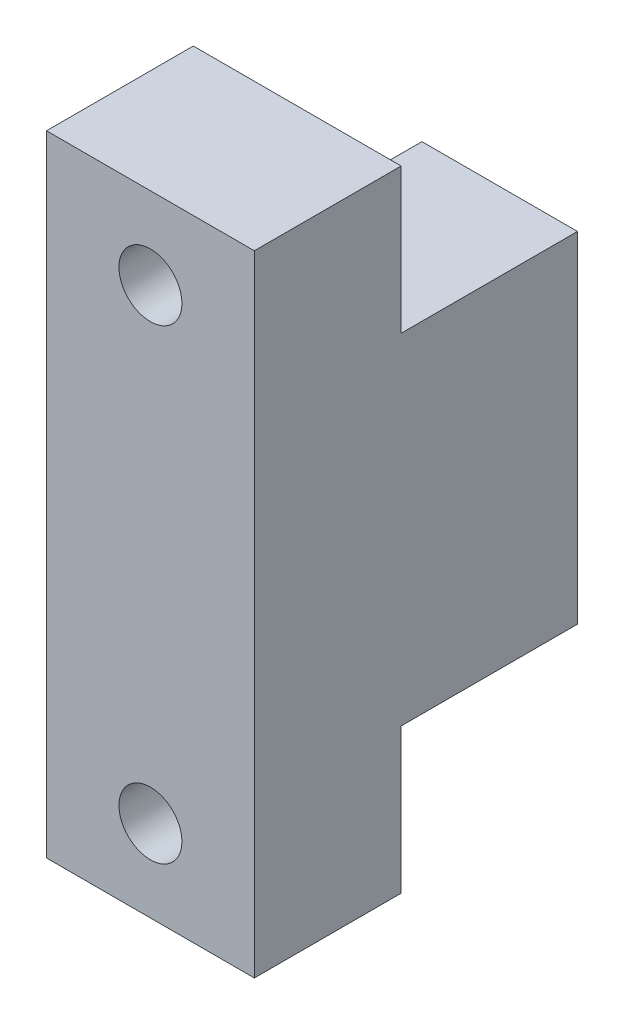
SolidWorks part; units mm, degrees
ref_plane "Front Plane" through (0, 0, 0) normal (0, 0, 1) x (1, 0, 0)
ref_plane "Top Plane" through (0, 0, 0) normal (0, 1, 0) x (1, 0, 0)
ref_plane "Right Plane" through (0, 0, 0) normal (1, 0, 0) x (0, 0, -1)
sketch "Sketch2" plane through (0, 0, 0) normal (0, 0, 1) x (1, 0, 0)
  line L0 (5.5262, -15.0933) -> (5.5262, 34.9067)
  line L1 (-10.9738, -15.0933) -> (5.5262, -15.0933)
  line L2 (-10.9738, 34.9067) -> (5.5262, 34.9067)
  line L23 (-10.9738, 34.9067) -> (-10.9738, -15.0933)
  circle A2 centre (-2.7238, -8.5933) radius 2.5
  circle A3 centre (-2.7238, 28.4067) radius 2.5
  dimension "D1" = 5
  dimension "D3" = 5
  dimension "D2" = 6.5
  dimension "D4" = 50
  dimension "D5" = 6.5
extrude "Boss-Extrude1" add sketch "Sketch2" along normal blind 11.655
sketch "Sketch4" plane through (0, 0, 11.655) normal (0, 0, 1) x (1, 0, 0)
  circle A31 centre (-2.7238, 28.4067) radius 4.5
  circle A32 centre (-2.7238, 28.4067) radius 4.5
  circle A34 centre (-2.7238, -8.5933) radius 4.5
  circle A35 centre (-2.7238, -8.5933) radius 4.5
  dimension "D1" = 2
  dimension "D2" = 2
extrude "Cut-Extrude3" cut sketch "Sketch4" against normal blind 10 from offset 7 offset against normal yes
sketch "Sketch6" plane through (0, 0, 0) normal (0, 0, -1) x (-1, 0, 0)
  line L0 (10.9738, 34.9067) -> (10.9738, -15.0933) construction
  line L1 (6.8238, 23.4067) -> (-5.5262, 23.4067)
  line L3 (6.8238, -3.5933) -> (6.8238, 23.4067)
  line L4 (6.8238, -3.5933) -> (-5.5262, -3.5933)
  line L6 (-5.5262, 23.4067) -> (-5.5262, -3.5933)
  point P4 (0, 0)
  point P12 (6.8238, -3.9751)
  dimension "D2" = 4.15
  dimension "D4" = 16.5
  dimension "D5" = 11.5
  dimension "D8" = 38.5
extrude "Boss-Extrude2" add sketch "Sketch6" along normal up to surface (6 mm away)
sketch "Sketch7" plane through (0, 0, -6) normal (0, 0, -1) x (-1, 0, 0)
  circle A2 centre (2.7238, 17.9067) radius 2.1
  circle A3 centre (2.7238, 1.9067) radius 2.1
  dimension "D1" = 4.2
  dimension "D2" = 4.2
extrude "Cut-Extrude4" cut sketch "Sketch7" against normal blind 6
chamfer "Chamfer1" distance 1 angle 45 2 edges at (-4.8238, 1.9067, -6) (-4.8238, 17.9067, -6)
sketch "Sketch8" plane through (0, 0, -6) normal (0, 0, -1) x (-1, 0, 0)
  line L5 (6.8238, 23.4067) -> (6.8238, -3.5933) construction
  line L6 (6.8238, 21.8067) -> (6.8238, 23.4067)
  line L7 (6.8238, 23.4067) -> (-5.5262, 23.4067)
  line L8 (-5.5262, 23.4067) -> (-5.5262, -3.5933)
  line L9 (-5.5262, -3.5933) -> (6.8238, -3.5933)
  line L10 (6.8238, -3.5933) -> (-5.5262, -3.5933) construction
  line L11 (6.8238, -1.9933) -> (2.7238, -1.9933)
  line L12 (-1.1762, 1.9067) -> (-1.1762, 17.9067)
  line L13 (2.7238, 21.8067) -> (6.8238, 21.8067)
  line L14 (6.8238, -3.5933) -> (6.8238, -1.9933)
  arc A7 (-1.1762, 1.9067) -> (2.7238, -1.9933) centre (2.7238, 1.9067) ccw
  arc A8 (2.7238, 21.8067) -> (-1.1762, 17.9067) centre (2.7238, 17.9067) ccw
extrude "Boss-Extrude3" add sketch "Sketch8" along normal blind 8
